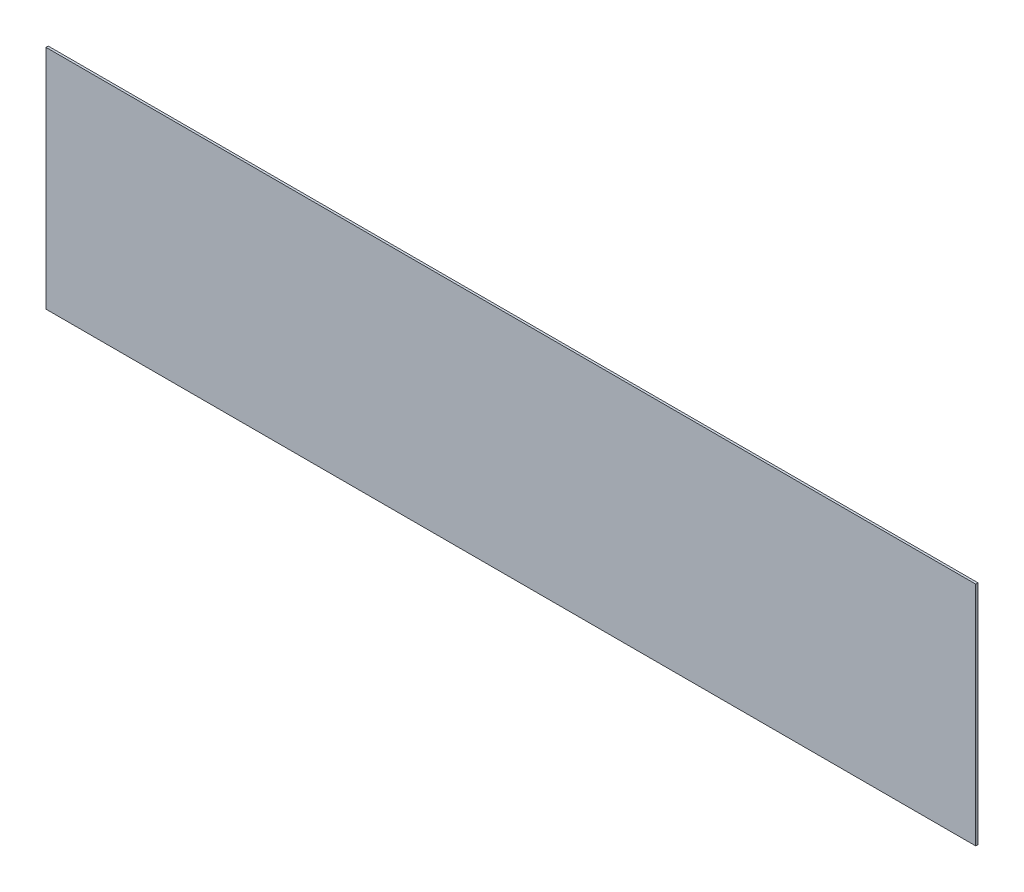
SolidWorks part; units mm, degrees
material "Acrílico (médio-alto impacto)"
ref_plane "Plano frontal" through (0, 0, 0) normal (0, 0, 1) x (1, 0, 0)
ref_plane "Plano superior" through (0, 0, 0) normal (0, 1, 0) x (1, 0, 0)
ref_plane "Plano direito" through (0, 0, 0) normal (1, 0, 0) x (0, 0, -1)
sketch "Esboço1" plane through (0, 0, 0) normal (0, 0, 1) x (1, 0, 0)
  line L1 (-820, -200) -> (820, -200)
  line L2 (-820, -200) -> (-820, 200)
  line L3 (-820, 200) -> (820, 200)
  line L4 (820, -200) -> (820, 200)
  line L5 (-820, -200) -> (820, 200) construction
  line L6 (-820, 200) -> (820, -200) construction
  point P0 (0, 0)
  dimension "D1" = 1640
  dimension "D2" = 400
extrude "Ressalto-extrusão1" add sketch "Esboço1" along normal blind 4
